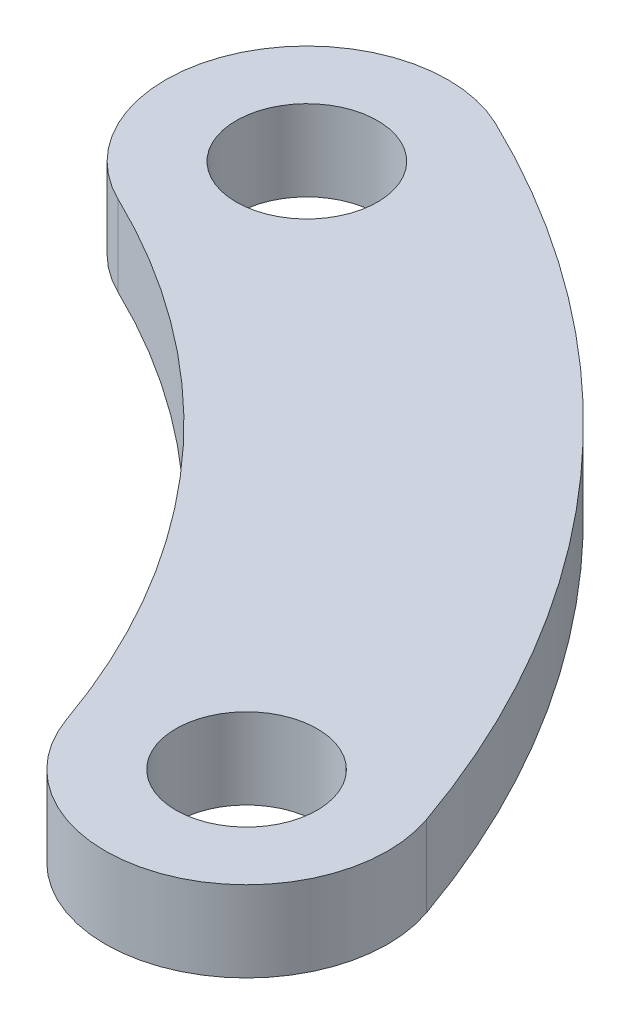
SolidWorks part; units mm, degrees
ref_plane "Front Plane" through (0, 0, 0) normal (0, 0, 1) x (1, 0, 0)
ref_plane "Top Plane" through (0, 0, 0) normal (0, 1, 0) x (1, 0, 0)
ref_plane "Right Plane" through (0, 0, 0) normal (1, 0, 0) x (0, 0, -1)
sketch "Sketch1" plane through (0, 2, 0) normal (0, 1, 0) x (1, 0, 0)
  line L0 (0, 0) -> (22.8034, 7.9515) construction
  line L1 (0, 0) -> (10.5019, 21.747) construction
  circle A10 centre (0, 0) radius 24.15 construction
  arc A12 (10.5019, 21.747) -> (22.8034, 7.9515) centre (0, 0) cw construction
  arc A13 (26.1083, 9.1038) -> (12.024, 24.8987) centre (0, 0) ccw
  arc A14 (19.4986, 6.7991) -> (8.9799, 18.5953) centre (0, 0) ccw
  arc A15 (19.4986, 6.7991) -> (26.1083, 9.1038) centre (22.8034, 7.9515) ccw
  arc A16 (12.024, 24.8987) -> (8.9799, 18.5953) centre (10.5019, 21.747) ccw
  circle A17 centre (10.5019, 21.747) radius 1.75
  circle A18 centre (22.8034, 7.9515) radius 1.75
  point P16 (18.0247, 16.0727)
  dimension "D1" = 48.3
  dimension "D2" = 45
  dimension "D3" = 3.5
  dimension "D4" = 3.5
  dimension "D5" = 3.5
extrude "Boss-Extrude1" add sketch "Sketch1" along normal blind 2
